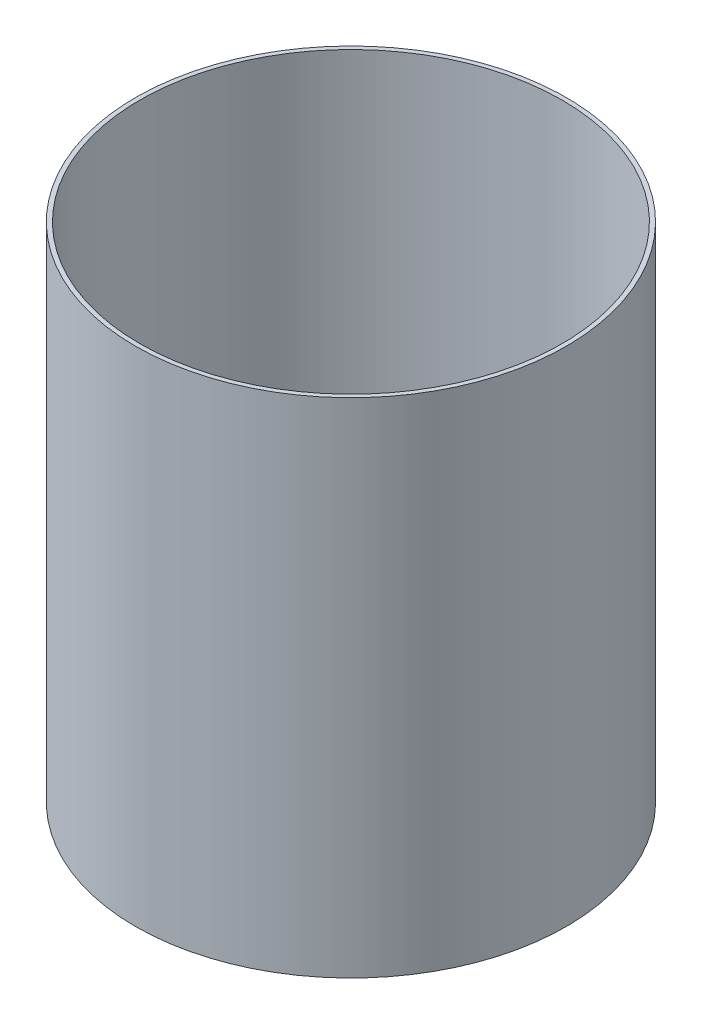
SolidWorks part; units mm, degrees
ref_plane "Front Plane" through (0, 0, 0) normal (0, 0, 1) x (1, 0, 0)
ref_plane "Top Plane" through (0, 0, 0) normal (0, 1, 0) x (1, 0, 0)
ref_plane "Right Plane" through (0, 0, 0) normal (1, 0, 0) x (0, 0, -1)
sketch "Sketch2" plane through (0, 0, 0) normal (0, 0, 1) x (1, 0, 0)
  line L0 (0, 64.0982) -> (0, -113.7018) construction
  line L1 (-76.2, 64.0982) -> (-74.676, 64.0982)
  line L2 (-76.2, 64.0982) -> (-76.2, -113.7018)
  line L3 (-76.2, -113.7018) -> (-74.676, -113.7018)
  line L4 (-74.676, 64.0982) -> (-74.676, -113.7018)
  dimension "D1" = 177.8
  dimension "D2" = 1.524
  dimension "D3" = 76.2
revolve "Revolve1" add sketch "Sketch2" angle 360 about L0
